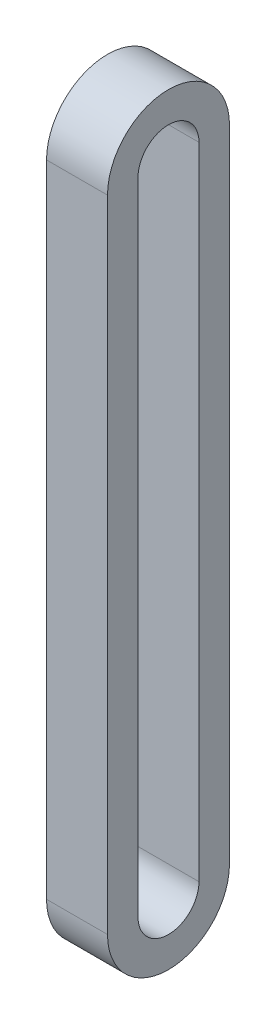
SolidWorks part; units mm, degrees
ref_plane "Front Plane" through (0, 0, 0) normal (0, 0, 1) x (1, 0, 0)
ref_plane "Top Plane" through (0, 0, 0) normal (0, 1, 0) x (1, 0, 0)
ref_plane "Right Plane" through (0, 0, 0) normal (1, 0, 0) x (0, 0, -1)
sketch "Sketch2" plane through (20, 0, 0) normal (1, 0, 0) x (0, 0, -1)
  line L0 (0, 130) -> (0, 25) construction
  line L1 (10, 130) -> (10, 25)
  line L2 (-10, 130) -> (-10, 25)
  line L3 (-57.5, 10) -> (57.5, 10) construction
  line L4 (0, 130) -> (0, 25) construction
  line L5 (5, 130) -> (5, 25)
  line L6 (-5, 130) -> (-5, 25)
  arc A0 (10, 130) -> (-10, 130) centre (0, 130) ccw
  arc A1 (-10, 25) -> (10, 25) centre (0, 25) ccw
  arc A2 (5, 130) -> (-5, 130) centre (0, 130) ccw
  arc A3 (-5, 25) -> (5, 25) centre (0, 25) ccw
  point P4 (0, 77.5)
  point P9 (0, 77.5)
  dimension "D1" = 10
  dimension "D4" = 5
  dimension "D3" = 15
extrude "Boss-Extrude2" add sketch "Sketch2" along normal blind 10 contours L5 A3 L6 A2 | A0 L2 A1 L1
